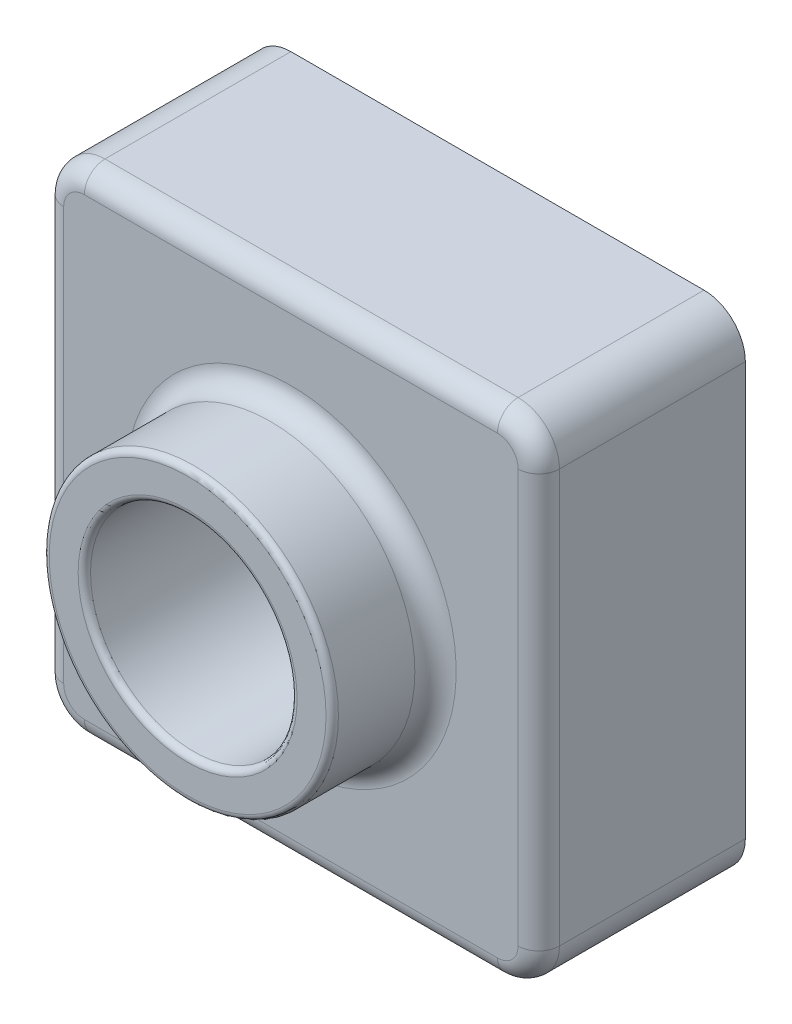
SolidWorks part; units mm, degrees
material "Chrome Stainless Steel"
ref_plane "Front Plane" through (0, 0, 0) normal (0, 0, 1) x (1, 0, 0)
ref_plane "Top Plane" through (0, 0, 0) normal (0, 1, 0) x (1, 0, 0)
ref_plane "Right Plane" through (0, 0, 0) normal (1, 0, 0) x (0, 0, -1)
sketch "Sketch1" plane through (0, 0, 0) normal (0, 0, 1) x (1, 0, 0)
  line L1 (-60, -60) -> (60, -60)
  line L2 (-60, -60) -> (-60, 60)
  line L3 (-60, 60) -> (60, 60)
  line L4 (60, -60) -> (60, 60)
  line L5 (-60, -60) -> (60, 60) construction
  line L6 (-60, 60) -> (60, -60) construction
  point P0 (0, 0)
  dimension "D1" = 120
  dimension "D2" = 120
extrude "Boss-Extrude1" add sketch "Sketch1" along normal blind 50
sketch "Sketch2" plane through (0, 0, 50) normal (0, 0, 1) x (1, 0, 0)
  circle A0 centre (0, 0) radius 35
  dimension "D1" = 70
extrude "Boss-Extrude2" add sketch "Sketch2" along normal blind 25
sketch "Sketch3" plane through (0, 0, 75) normal (0, 0, 1) x (1, 0, 0)
  circle A0 centre (0, 0) radius 25
  dimension "D1" = 50
extrude "Cut-Extrude1" cut sketch "Sketch3" against normal through all
fillet "Fillet1" radius 1.5 2 edges at (25, 0, 75) (35, 0, 75)
fillet "Fillet2" radius 10 4 edges at (-60, -60, 25) (-60, 60, 25) (60, -60, 25) (60, 60, 25)
fillet "Fillet4" radius 5 9 edges at (-57.0711, 57.0711, 50) (0, 60, 50) (57.0711, 57.0711, 50) (60, 0, 50) (57.0711, -57.0711, 50) (0, -60, 50) (-57.0711, -57.0711, 50) (35, 0, 50) (-60, 0, 50)
shell "Shell1" thickness 2
